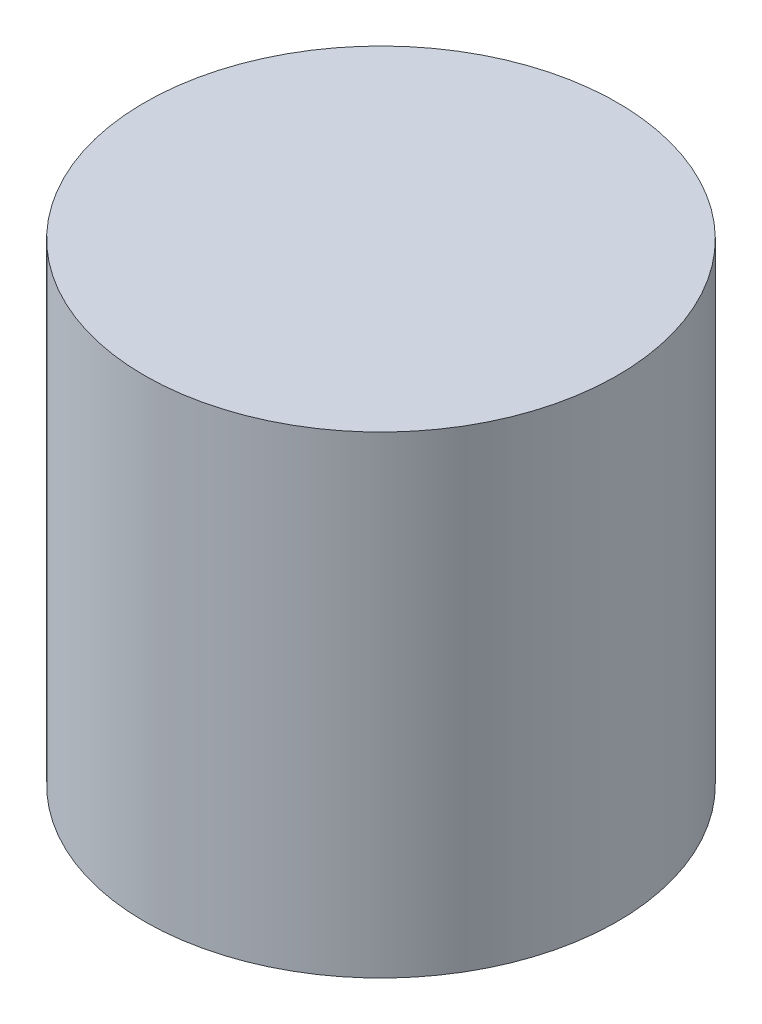
SolidWorks part; units mm, degrees
ref_plane "Front" through (0, 0, 0) normal (0, 0, 1) x (1, 0, 0)
ref_plane "Top" through (0, 0, 0) normal (0, 1, 0) x (1, 0, 0)
ref_plane "Right" through (0, 0, 0) normal (1, 0, 0) x (0, 0, -1)
sketch "Sketch1" plane through (0, 0, 0) normal (0, 1, 0) x (1, 0, 0)
  circle A0 centre (0, 0) radius 15
  dimension "D1" = 30
extrude "Boss-Extrude1" add sketch "Sketch1" along normal blind 30
